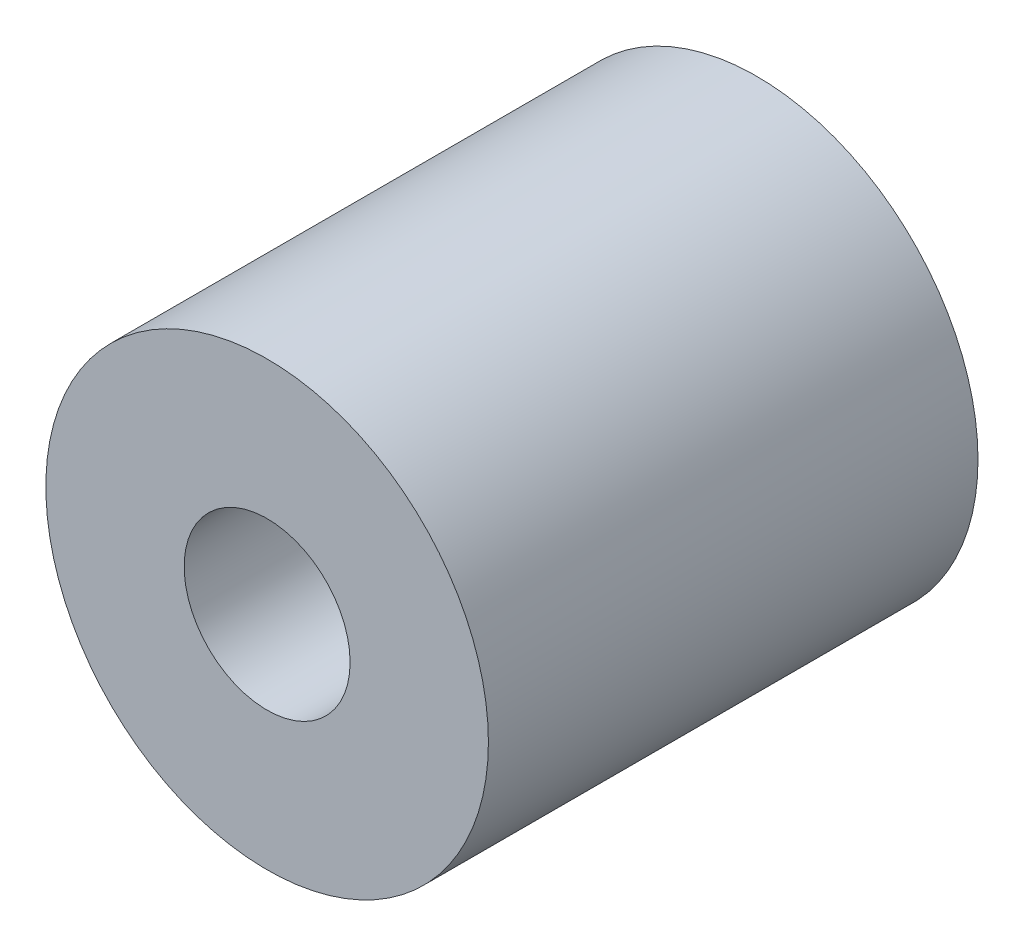
SolidWorks part; units mm, degrees
material "AISI 1020"
ref_plane "Alzado" through (0, 0, 0) normal (0, 0, 1) x (1, 0, 0)
ref_plane "Planta" through (0, 0, 0) normal (0, 1, 0) x (1, 0, 0)
ref_plane "Vista lateral" through (0, 0, 0) normal (1, 0, 0) x (0, 0, -1)
sketch "Croquis1" plane through (0, 0, 0) normal (0, 0, 1) x (1, 0, 0)
  circle A0 centre (0, 0) radius 16
  circle A1 centre (0, 0) radius 11
  dimension "D1" = 32
  dimension "D2" = 22
extrude "Saliente-Extruir1" add sketch "Croquis1" along normal blind 19
sketch "Croquis2" plane through (0, 0, 19) normal (0, 0, 1) x (1, 0, 0)
  circle A0 centre (0, 0) radius 16
  circle A1 centre (0, 0) radius 6
  dimension "D1" = 32
  dimension "D2" = 12
extrude "Saliente-Extruir2" add sketch "Croquis2" along normal blind 16.4
